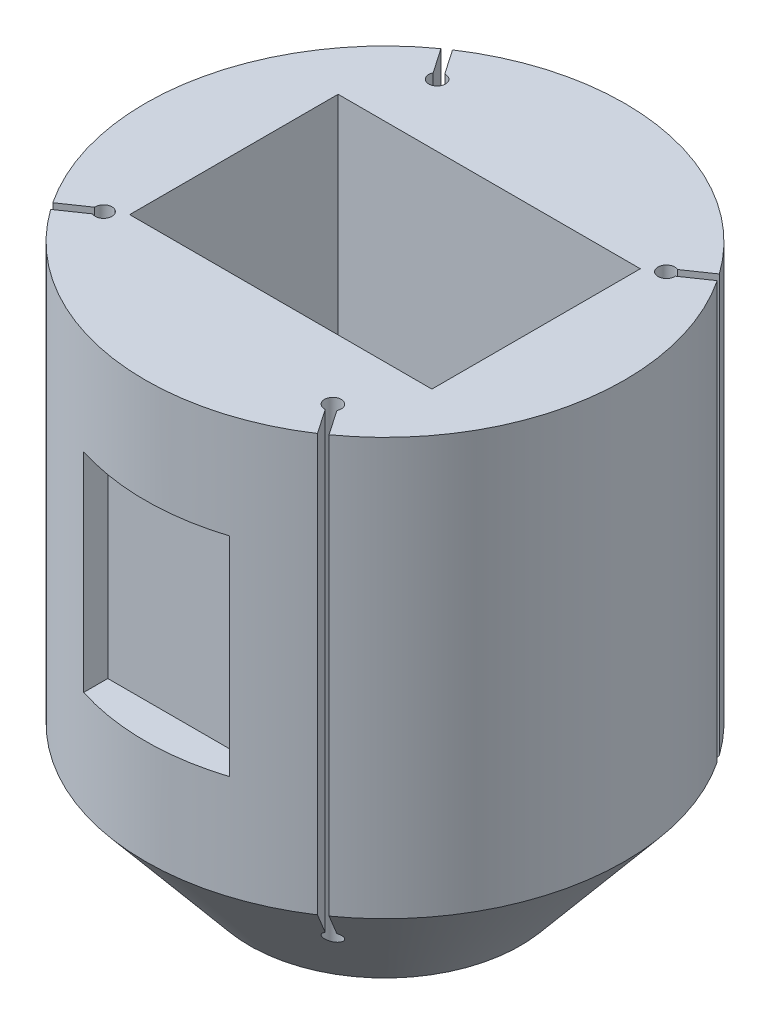
SolidWorks part; units mm, degrees
ref_plane "Piano frontale" through (0, 0, 0) normal (0, 0, 1) x (1, 0, 0)
ref_plane "Piano superiore" through (0, 0, 0) normal (0, 1, 0) x (1, 0, 0)
ref_plane "Piano destro" through (0, 0, 0) normal (1, 0, 0) x (0, 0, -1)
sketch "Schizzo1" plane through (0, 0, 0) normal (0, 0, 1) x (1, 0, 0)
  line L0 (-21.0825, 47.7284) -> (93.9175, 47.7284)
  line L1 (-21.0825, 47.7284) -> (-21.0825, -212.2716)
  line L2 (93.9175, 47.7284) -> (93.9175, -152.2716)
  line L4 (-21.0825, -212.2716) -> (43.9175, -212.2716)
  line L5 (43.9175, -212.2716) -> (93.9175, -152.2716)
revolve "Rivoluzione1" add sketch "Schizzo1" angle 360 about L1
sketch "Schizzo2" plane through (0, 47.7284, 0) normal (0, 1, 0) x (1, 0, 0)
  line L0 (60.639, 58.6106) -> (72.535, 66.789)
  line L3 (62.9051, 55.3144) -> (74.8011, 63.4929)
  line L4 (37.5281, -81.7215) -> (45.7066, -93.6174)
  line L5 (34.2319, -83.9876) -> (42.4104, -95.8835)
  line L7 (-102.804, -58.6106) -> (-114.6999, -66.789)
  line L8 (-79.6931, 81.7215) -> (-87.8715, 93.6174)
  line L9 (-76.3969, 83.9876) -> (-84.5754, 95.8835)
  line L11 (-105.0701, -55.3144) -> (-116.966, -63.4929)
  arc A0 (60.639, 58.6106) -> (62.9051, 55.3144) centre (58.9175, 55) ccw
  arc A1 (74.8011, 63.4929) -> (72.535, 66.789) centre (-21.0825, 0) ccw
  arc A2 (-79.6931, 81.7215) -> (-76.3969, 83.9876) centre (-76.0825, 80) ccw
  arc A4 (-84.5754, 95.8835) -> (-87.8715, 93.6174) centre (-21.0825, 0) ccw
  arc A5 (45.7066, -93.6174) -> (42.4104, -95.8835) centre (-21.0825, 0) cw
  arc A6 (34.2319, -83.9876) -> (37.5281, -81.7215) centre (33.9175, -80) cw
  arc A7 (-114.6999, -66.789) -> (-116.966, -63.4929) centre (-21.0825, 0) cw
  arc A9 (-105.0701, -55.3144) -> (-102.804, -58.6106) centre (-101.0825, -55) cw
extrude "Taglio-Estrusione1" cut sketch "Schizzo2" against normal up to next
sketch "Schizzo3" plane through (0, 47.7284, 0) normal (0, 1, 0) x (1, 0, 0)
  line L5 (-93.5825, 50) -> (51.4175, 50)
  line L6 (-93.5825, 50) -> (-93.5825, -50)
  line L7 (-93.5825, -50) -> (51.4175, -50)
  line L8 (51.4175, 50) -> (51.4175, -50)
  line L9 (-93.5825, 50) -> (51.4175, -50) construction
  line L10 (-93.5825, -50) -> (51.4175, 50) construction
extrude "Taglio-Estrusione2" cut sketch "Schizzo3" against normal blind 100
sketch "Schizzo4" plane through (0, 47.7284, 0) normal (0, 1, 0) x (1, 0, 0)
  circle A1 centre (-71.0825, 0) radius 4
  circle A2 centre (28.9175, 0) radius 4
extrude "Taglio-Estrusione3" cut sketch "Schizzo4" against normal blind 250
sketch "Schizzo5" plane through (0, 47.7284, 0) normal (0, 1, 0) x (1, 0, 0)
  line L1 (-21.0825, -115) -> (-21.0825, -98)
  circle A0 centre (-21.0825, 0) radius 115
ref_plane "Piano1" through (0, 0, 98) normal (0, 0, 1) x (1, 0, 0)
sketch "Schizzo6" plane through (0, 0, 98) normal (0, 0, 1) x (1, 0, 0)
  line L5 (13.9175, -2.2716) -> (-56.0825, -2.2716)
  line L6 (13.9175, -2.2716) -> (13.9175, -102.2716)
  line L7 (13.9175, -102.2716) -> (-56.0825, -102.2716)
  line L8 (-56.0825, -2.2716) -> (-56.0825, -102.2716)
  line L9 (13.9175, -2.2716) -> (-56.0825, -102.2716) construction
  line L10 (13.9175, -102.2716) -> (-56.0825, -2.2716) construction
extrude "Taglio-Estrusione4" cut sketch "Schizzo6" along normal through all
